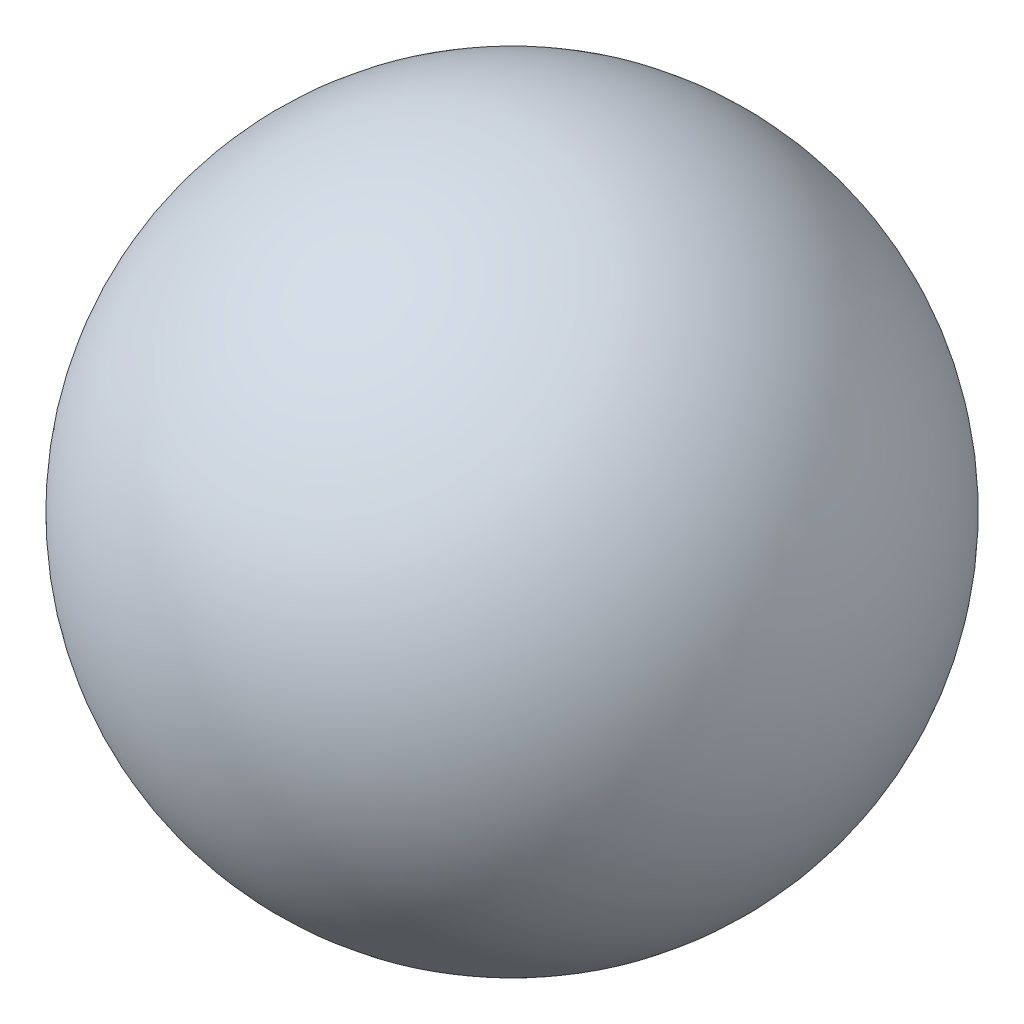
SolidWorks part; units mm, degrees
ref_plane "Front Plane" through (0, 0, 0) normal (0, 0, 1) x (1, 0, 0)
ref_plane "Top Plane" through (0, 0, 0) normal (0, 1, 0) x (1, 0, 0)
ref_plane "Right Plane" through (0, 0, 0) normal (1, 0, 0) x (0, 0, -1)
sketch "Sketch1" plane through (0, 0, 0) normal (0, 0, 1) x (1, 0, 0)
  line L0 (0, 11.25) -> (0, -11.25) construction
  line L1 (0, 11.25) -> (0, -11.25)
  arc A0 (0, 11.25) -> (0, -11.25) centre (0, 0) cw
  point P5 (0, 0)
  point P6 (0, 0)
  point P7 (0, -10.9598)
  point P8 (0, 0)
  point P9 (0, 0)
  dimension "D1" = 11.25
revolve "Revolve1" add sketch "Sketch1" angle 360 about L0
